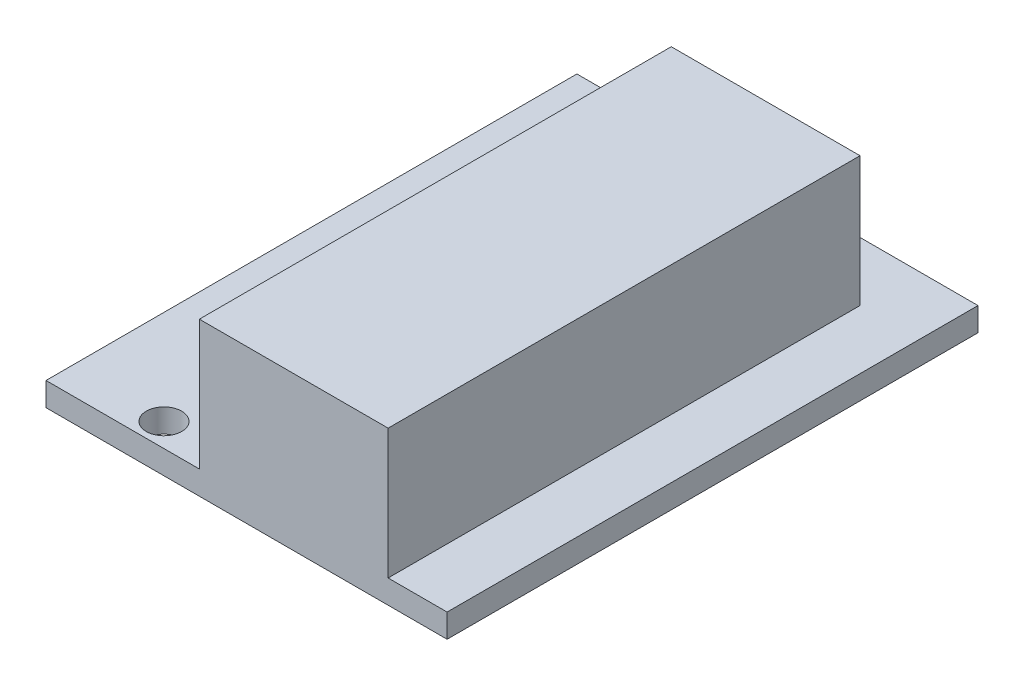
SolidWorks part; units mm, degrees
ref_plane "Front Plane" through (0, 0, 0) normal (0, 0, 1) x (1, 0, 0)
ref_plane "Top Plane" through (0, 0, 0) normal (0, 1, 0) x (1, 0, 0)
ref_plane "Right Plane" through (0, 0, 0) normal (1, 0, 0) x (0, 0, -1)
sketch "Sketch1" plane through (0, 0, 0) normal (0, 1, 0) x (1, 0, 0)
  line L1 (-17, -56) -> (17, -56)
  line L2 (-17, -56) -> (-17, 56)
  line L3 (-17, 56) -> (17, 56)
  line L4 (17, -56) -> (17, 56)
  line L5 (-17, -56) -> (17, 56) construction
  line L6 (-17, 56) -> (17, -56) construction
  circle A0 centre (13.6, -52.6) radius 1.5
  circle A1 centre (-9, 49) radius 1.5
  circle A2 centre (-9, 13) radius 1.5
  point P0 (0, 0)
  point P12 (-12, 22.7848)
  point P13 (0, 0)
  dimension "D3" = 3
  dimension "D6" = 3
  dimension "D7" = 8
  dimension "D10" = 3
  dimension "D1" = 112
  dimension "D2" = 34
  dimension "D4" = 3.4
  dimension "D5" = 3.4
  dimension "D8" = 7
  dimension "D9" = 43
extrude "Board" add sketch "Sketch1" along normal blind 2
sketch "Sketch2" plane through (0, 2, 0) normal (0, 1, 0) x (1, 0, 0)
  line L0 (17, 56) -> (-17, 56) construction
  line L1 (12, 51) -> (-4, 51)
  line L2 (12, 51) -> (12, 11)
  line L3 (12, 11) -> (-4, 11)
  line L4 (-4, 51) -> (-4, 11)
  line L5 (12, 51) -> (-4, 11) construction
  line L6 (12, 11) -> (-4, 51) construction
  line L7 (17, -56) -> (17, 56) construction
  line L9 (5, 10) -> (11, 10)
  line L10 (5, 10) -> (5, 0)
  line L11 (5, 0) -> (11, 0)
  line L12 (11, 10) -> (11, 0)
  line L13 (5, 10) -> (11, 0) construction
  line L14 (5, 0) -> (11, 10) construction
  point P4 (4, 31)
  point P13 (8, 5)
  dimension "D1" = 40
  dimension "D2" = 16
  dimension "D3" = 5
  dimension "D4" = 5
  dimension "D5" = 10
  dimension "D6" = 6
  dimension "D7" = 6
  dimension "D8" = 46
extrude "7SEG" add sketch "Sketch2" along normal blind 11
sketch "Sketch3" plane through (0, 2, 0) normal (0, 1, 0) x (1, 0, 0)
  line L0 (17, 56) -> (-17, 56) construction
  line L1 (-7, 36) -> (3, 36)
  line L2 (-7, 36) -> (-7, 16)
  line L3 (-7, 16) -> (3, 16)
  line L4 (3, 36) -> (3, 16)
  line L5 (-7, 36) -> (3, 16) construction
  line L6 (-7, 16) -> (3, 36) construction
  line L7 (-17, 56) -> (-17, -56) construction
  line L9 (-1, 10) -> (9, 10)
  line L10 (-1, 10) -> (-1, 0)
  line L11 (-1, 0) -> (9, 0)
  line L12 (9, 10) -> (9, 0)
  line L13 (-1, 10) -> (9, 0) construction
  line L14 (-1, 0) -> (9, 10) construction
  line L15 (-1, -12) -> (9, -12)
  line L16 (-1, -12) -> (-1, -22)
  line L17 (-1, -22) -> (9, -22)
  line L18 (9, -12) -> (9, -22)
  line L19 (-1, -12) -> (9, -22) construction
  line L20 (-1, -22) -> (9, -12) construction
  point P4 (-2, 26)
  point P13 (4, 5)
  point P18 (4, -17)
  point P19 (-1, -17)
  dimension "D1" = 20
  dimension "D2" = 10
  dimension "D3" = 20
  dimension "D4" = 10
  dimension "D5" = 10
  dimension "D6" = 46
  dimension "D7" = 16
  dimension "D8" = 10
  dimension "D9" = 16
  dimension "D10" = 68
extrude "IC" add sketch "Sketch3" along normal blind 8
sketch "Sketch5" plane through (0, 2, 0) normal (0, 1, 0) x (1, 0, 0)
  line L0 (17, -56) -> (17, 56) construction
  line L1 (2, -6) -> (11, -6)
  line L2 (2, -6) -> (2, -23)
  line L3 (2, -23) -> (11, -23)
  line L4 (11, -6) -> (11, -23)
  line L5 (2, -6) -> (11, -23) construction
  line L6 (2, -23) -> (11, -6) construction
  line L7 (-1, 0) -> (11, 0) construction
  point P4 (6.5, -14.5)
  dimension "D1" = 17
  dimension "D2" = 9
  dimension "D3" = 6
  dimension "D4" = 6
extrude "BienTroA" add sketch "Sketch5" along normal blind 23
sketch "Sketch6" plane through (11, 0, 0) normal (1, 0, 0) x (0, 0, -1)
  line L0 (-23, 25) -> (-6, 25) construction
  circle A0 centre (-14.5, 16.6) radius 3.4
  point P9 (-14.5, 25)
  dimension "D1" = 6.8
  dimension "D2" = 8.4
extrude "BienTroB" add sketch "Sketch6" along normal blind 15
sketch "Sketch7" plane through (0, 2, 0) normal (0, 1, 0) x (1, 0, 0)
  line L0 (-17, -56) -> (17, -56) construction
  line L1 (10, -50) -> (0, -50)
  line L2 (10, -50) -> (10, -45)
  line L3 (10, -45) -> (0, -45)
  line L4 (0, -50) -> (0, -45)
  line L5 (10, -50) -> (0, -45) construction
  line L6 (10, -45) -> (0, -50) construction
  line L7 (17, -56) -> (17, 56) construction
  point P4 (5, -47.5)
  dimension "D1" = 5
  dimension "D2" = 10
  dimension "D3" = 6
  dimension "D4" = 7
extrude "IRF540" add sketch "Sketch7" along normal blind 26
sketch "Sketch8" plane through (0, 2, 0) normal (0, 1, 0) x (1, 0, 0)
  line L0 (-17, -56) -> (17, -56) construction
  line L1 (-11, -45) -> (6, -45)
  line L2 (-11, -45) -> (-11, -55)
  line L3 (-11, -55) -> (6, -55)
  line L4 (6, -45) -> (6, -55)
  line L5 (-11, -45) -> (6, -55) construction
  line L6 (-11, -55) -> (6, -45) construction
  line L7 (-17, 56) -> (-17, -56) construction
  point P4 (-2.5, -50)
  dimension "D1" = 10
  dimension "D2" = 17
  dimension "D3" = 1
  dimension "D4" = 6
extrude "Domino" add sketch "Sketch8" along normal blind 10
sketch "Sketch9" plane through (0, 2, 0) normal (0, 1, 0) x (1, 0, 0)
  line L0 (-17, 56) -> (-17, -56) construction
  line L1 (-2, -41) -> (-24, -41)
  line L2 (-2, -41) -> (-2, -11)
  line L3 (-2, -11) -> (-24, -11)
  line L4 (-24, -41) -> (-24, -11)
  line L5 (-2, -41) -> (-24, -11) construction
  line L6 (-2, -11) -> (-24, -41) construction
  line L7 (-17, -56) -> (17, -56) construction
  point P4 (-13, -26)
  dimension "D1" = 30
  dimension "D2" = 22
  dimension "D3" = 7
  dimension "D4" = 15
extrude "7805" add sketch "Sketch9" along normal blind 30
sketch "Sketch10" plane through (0, 2, 0) normal (0, 1, 0) x (1, 0, 0)
  line L0 (17, 11) -> (-17, 11)
  line L1 (17, -56) -> (17, 56) construction
  line L2 (-17, 56) -> (-17, -11) construction
split "Split2" trim tools "Sketch10" bodies to split 108 resulting bodies 110 111
delete or keep bodies "Body-Delete/Keep 1" type delete bodies bodies 111
